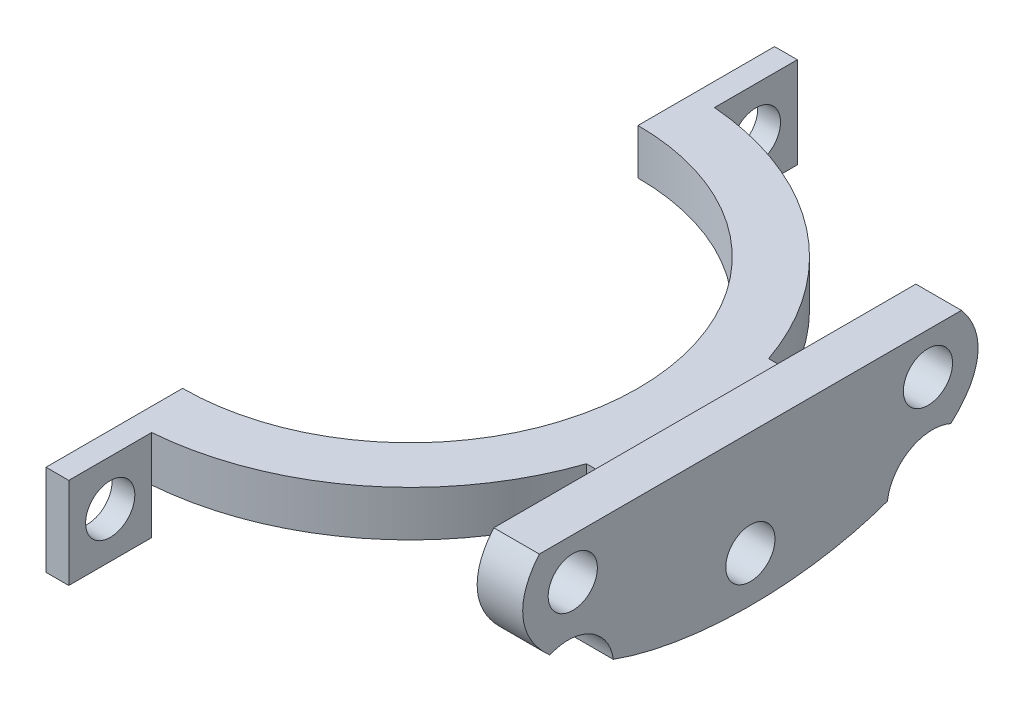
SolidWorks part; units mm, degrees
ref_plane "Front Plane" through (0, 0, 0) normal (0, 0, 1) x (1, 0, 0)
ref_plane "Top Plane" through (0, 0, 0) normal (0, 1, 0) x (1, 0, 0)
ref_plane "Right Plane" through (0, 0, 0) normal (1, 0, 0) x (0, 0, -1)
sketch "Sketch1" plane through (0, 0, 0) normal (0, 1, 0) x (1, 0, 0)
  line L0 (0, -25) -> (0, -40)
  line L1 (0, -55) -> (0, 55) construction
  line L2 (0, -40) -> (2.5, -40)
  line L3 (2.5, -40) -> (2.5, -24.8747)
  line L4 (-55, 0) -> (55, 0) construction
  line L5 (2.5, 40) -> (2.5, 24.8747)
  line L6 (0, 40) -> (2.5, 40)
  line L7 (0, 25) -> (0, 40)
  line L8 (0, 0) -> (38.571, 0) construction
  line L9 (37.3428, 10) -> (29.3428, 10)
  line L10 (37.3428, -10) -> (29.3428, -10)
  line L11 (37.3428, 10) -> (37.3428, -10)
  circle A0 centre (0, 0) radius 25
  circle A1 centre (0, 0) radius 31
  point P22 (33.3428, 10)
  dimension "D1" = 50
  dimension "D2" = 6
  dimension "D3" = 15
  dimension "D4" = 2.5
  dimension "D5" = 20
  dimension "D6" = 8
extrude "Boss-Extrude1" add sketch "Sketch1" along normal blind 5
sketch "Sketch2" plane through (0, 0, 0) normal (0, -1, 0) x (1, 0, 0)
  line L0 (0, 25) -> (0, 40) construction
  line L1 (0, 30.899) -> (2.5, 30.899)
  line L2 (0, 30.899) -> (0, 40)
  line L3 (0, 40) -> (2.5, 40)
  line L4 (2.5, 30.899) -> (2.5, 40)
  line L5 (0, 30.899) -> (2.5, 40) construction
  line L6 (0, 40) -> (2.5, 30.899) construction
  line L7 (55, 0) -> (-55, 0) construction
  line L8 (0, -40) -> (2.5, -40)
  line L9 (2.5, -30.899) -> (2.5, -40)
  line L10 (0, -30.899) -> (2.5, -30.899)
  line L11 (0, -30.899) -> (0, -40)
  point P0 (1.25, 35.4495)
extrude "Boss-Extrude2" add sketch "Sketch2" along normal blind 5
sketch "Sketch3" plane through (0, 0, 0) normal (-1, 0, 0) x (0, 0, 1)
  line L0 (0, -5.5) -> (0, 5.5) construction
  line L1 (-30.899, -5) -> (-40, -5)
  line L2 (-30.899, -5) -> (-30.899, 5)
  line L3 (-30.899, 5) -> (-40, 5)
  line L4 (-40, -5) -> (-40, 5)
  line L5 (-30.899, -5) -> (-40, 5) construction
  line L6 (-30.899, 5) -> (-40, -5) construction
  circle A0 centre (-35.4495, 0) radius 2.7
  circle A1 centre (35.4495, 0) radius 2.7
  point P0 (-35.4495, 0)
  dimension "D1" = 5.4
extrude "Cut-Extrude1" cut sketch "Sketch3" against normal up to next contours A0 | A1
sketch "Sketch4" plane through (37.3428, 0, 0) normal (1, 0, 0) x (0, 0, -1)
  line L0 (10, 5) -> (-10, 5)
  line L1 (0, 5.5) -> (0, -5.5) construction
  line L2 (-10.2243, 2.5) -> (10.2243, 2.5)
  line L3 (10, 0) -> (-10, 0)
  line L4 (20.5385, 0) -> (-20.5385, 0) construction
  line L5 (-23.1756, 7) -> (23.1756, 7)
  line L6 (7.1085, 0) -> (-7.6211, 0) construction
  line L7 (7.1085, 5) -> (-7.6211, 5) construction
  line L8 (10, 5) -> (-10, 5) construction
  circle A0 centre (0, 9.5) radius 2.7
  circle A1 centre (0, -4.5) radius 2.7
  circle A4 centre (-19.5, 2.5) radius 2.7
  circle A5 centre (19.5, 2.5) radius 2.7
  ellipse E0 centre (0, 2.5) end of major axis (0, 14.5) minor radius 10.2243
  ellipse E1 centre (0, 2.5) end of major axis (25, 2.5) minor radius 12
  line M10 (-10, 0) -> (10, 0)
  line M11 (10, 0) -> (10, 5)
  line M12 (10, 5) -> (-10, 5)
  line M13 (-10, 5) -> (-10, 0)
  dimension "D3" = 5.4
  dimension "D6" = 5.4
  dimension "D1" = 12
  dimension "D2" = 25
  dimension "D4" = 5
  dimension "D5" = 5
  dimension "D7" = 5.5
  dimension "D8" = 2
extrude "Boss-Extrude3" add sketch "Sketch4" against normal blind 5 contours L5 E1 E0 A4 | L5 E0 M12 | E0 E1 L5 A5 | E0 A1 M10 | L2 E0 M11 | E0 L2 M11 | L2 E0 M13 | E0 L2 M13 | L5 A0
sketch "Sketch5" plane through (32.3428, 0, 0) normal (-1, 0, 0) x (0, 0, 1)
  circle A0 centre (-20, -7.7593) radius 5
  circle A1 centre (20, -7.7593) radius 5
extrude "Cut-Extrude2" cut sketch "Sketch5" against normal blind 10
